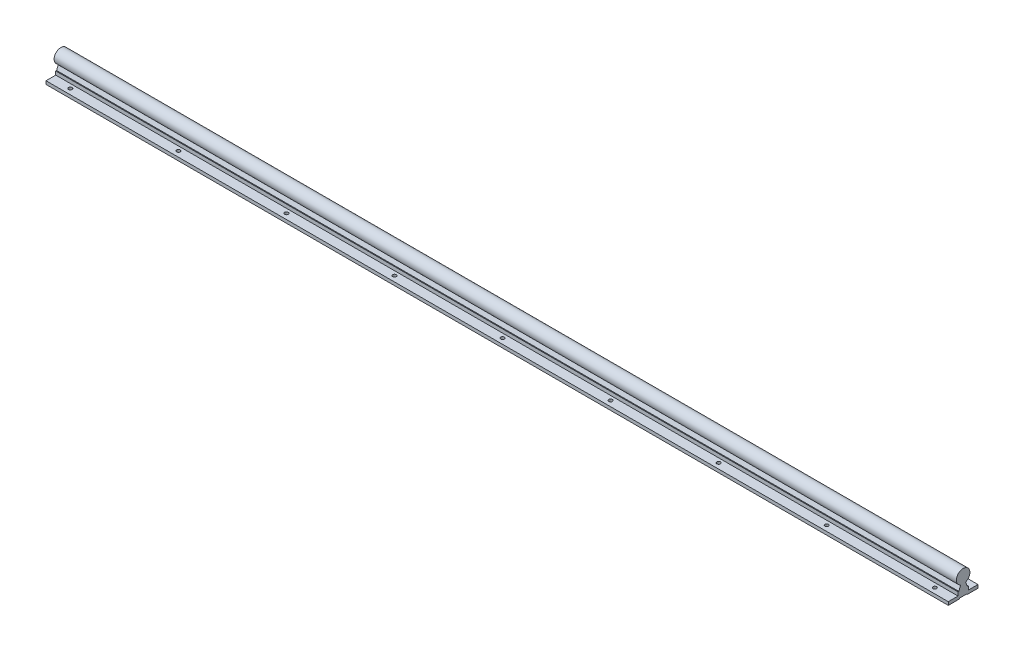
SolidWorks part; units mm, degrees
ref_plane "前视基准面" through (0, 0, 0) normal (0, 0, 1) x (1, 0, 0)
ref_plane "上视基准面" through (0, 0, 0) normal (0, 1, 0) x (1, 0, 0)
ref_plane "右视基准面" through (0, 0, 0) normal (1, 0, 0) x (0, 0, -1)
sketch "草图1" plane through (0, 0, 0) normal (1, 0, 0) x (0, 0, -1)
  line L0 (38.0237, 12.7102) -> (38.0237, 6.7102)
  line L1 (38.0237, 6.7102) -> (18.0237, 6.7102)
  line L2 (18.0237, 6.7102) -> (16.8237, 7.9102)
  line L3 (16.8237, 7.9102) -> (4.2237, 7.9102)
  line L4 (4.2237, 7.9102) -> (3.0237, 6.7102)
  line L5 (3.0237, 6.7102) -> (-16.9763, 6.7102)
  line L6 (-16.9763, 6.7102) -> (-16.9763, 12.7102)
  line L7 (-16.9763, 12.7102) -> (1.0237, 12.7102)
  line L8 (1.0237, 12.7102) -> (1.0237, 19.4102)
  line L9 (1.0237, 19.4102) -> (2.5937, 19.4102)
  line L10 (18.4537, 19.4102) -> (15.072, 28.0671)
  line L11 (38.0237, 12.7102) -> (20.0237, 12.7102)
  line L12 (20.0237, 12.7102) -> (20.0237, 19.4102)
  line L13 (20.0237, 19.4102) -> (18.4537, 19.4102)
  line L14 (2.5937, 19.4102) -> (5.9754, 28.0671)
  line L15 (10.5237, 7.9102) -> (10.5237, 59.2349) construction
  arc A0 (15.072, 28.0671) -> (5.9754, 28.0671) centre (10.5237, 39.7102) ccw
  dimension "D18" = 25
  dimension "D1" = 6
  dimension "D2" = 6
  dimension "D3" = 20
  dimension "D4" = 55
  dimension "D5" = 1.2
  dimension "D6" = 1.2
  dimension "D7" = 20
  dimension "D8" = 1.2
  dimension "D9" = 1.2
  dimension "D10" = 18
  dimension "D11" = 18
  dimension "D12" = 6.7
  dimension "D13" = 6.7
  dimension "D14" = 1.57
  dimension "D15" = 1.57
  dimension "D16" = 3.3817
  dimension "D17" = 3.3817
  dimension "D19" = 33
  dimension "D20" = 27.5
extrude "凸台-拉伸1" add sketch "草图1" along normal blind 1670
hole_wizard "Ø6.6 (6.6) 直径孔1" positions "3D草图1" profile "草图2" hole size "Ø6.6" standard "GB" end condition through all
sketch3d "3D草图1"
  line L0 (0, 12.7102, -38.0237) -> (0, 12.7102, -20.0237) construction
  line L1 (0, 12.7102, -1.0237) -> (0, 12.7102, 16.9763) construction
  line L2 (1670, 12.7102, -38.0237) -> (0, 12.7102, -38.0237) construction
  point P0 (35, 12.7102, -28.0237)
  point P2 (35, 12.7102, 6.9763)
  dimension "D1" = 35
  dimension "D2" = 35
  dimension "D3" = 35
  dimension "D4" = 10
sketch "草图2" plane through (35, 12.7102, -28.0237) normal (1, 0, 0) x (0, 0, 1)
  line L0 (0, 0) -> (0, 6)
  line L1 (0, 6) -> (3.3, 6)
  line L2 (3.3, 6) -> (3.3, 0)
  line L5 (3.3, 0) -> (0, 0)
  line L11 (0, -6.35) -> (0, 107.95) construction
  dimension "通孔孔直径" = 6.6
  dimension "通孔孔深度" = 6
pattern_linear "阵列(线性)1" count 9 spacing 200 along (1, 0, 0) of "Ø6.6 (6.6) 直径孔1"
